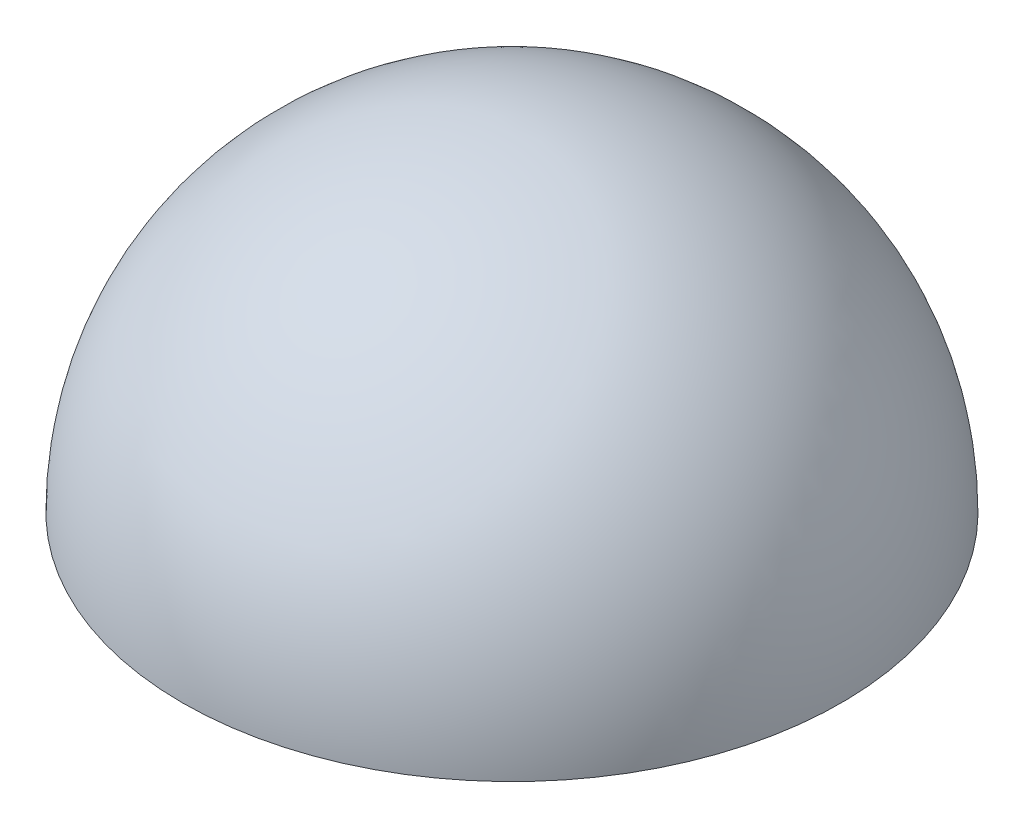
SolidWorks part; units mm, degrees
ref_plane "Ebene vorne" through (0, 0, 0) normal (0, 0, 1) x (1, 0, 0)
ref_plane "Ebene oben" through (0, 0, 0) normal (0, 1, 0) x (1, 0, 0)
ref_plane "Ebene rechts" through (0, 0, 0) normal (1, 0, 0) x (0, 0, -1)
sketch "Skizze1" plane through (0, 0, 0) normal (0, 1, 0) x (1, 0, 0)
  line L0 (0, 16.0729) -> (0, 7.5) construction
  line L1 (0, 12.5) -> (0, 7.5)
  line L2 (0, -7.5) -> (0, -20.8076) construction
  line L3 (0, -7.5) -> (0, -12.5)
  arc A0 (0, -7.5) -> (0, 7.5) centre (0, 0) ccw
  arc A1 (0, -12.5) -> (0, 12.5) centre (0, 0) ccw
  point P0 (0, 0)
  point P10 (0, 7.5)
  point P11 (0, -7.5)
  dimension "D1" = 25
  dimension "D2" = 15
revolve "Rotation1" add sketch "Skizze1" angle 180 about L0
